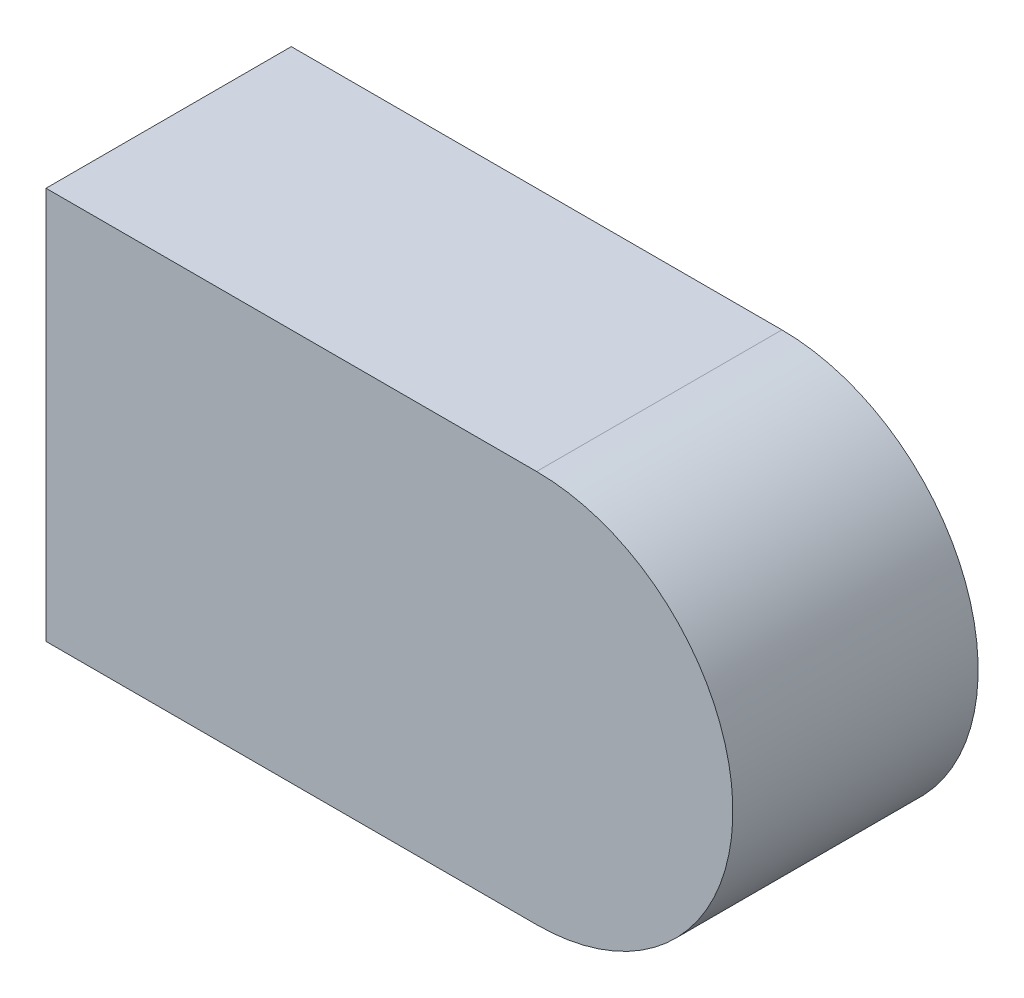
SolidWorks part; units mm, degrees
material "ABS"
ref_plane "Front Plane" through (0, 0, 0) normal (0, 0, 1) x (1, 0, 0)
ref_plane "Top Plane" through (0, 0, 0) normal (0, 1, 0) x (1, 0, 0)
ref_plane "Right Plane" through (0, 0, 0) normal (1, 0, 0) x (0, 0, -1)
sketch "Sketch1" plane through (0, 0, 0) normal (0, 0, 1) x (1, 0, 0)
  line L0 (-250, 192.5) -> (-200, 192.5) construction
  line L1 (-200, 232.5) -> (-250, 232.5) construction
  line L2 (-200, 232.5) -> (-250, 232.5)
  line L3 (-250, 192.5) -> (-200, 192.5)
  line L4 (-250, 232.5) -> (-250, 192.5)
  arc A0 (-200, 192.5) -> (-200, 232.5) centre (-200, 212.5) ccw construction
  arc A2 (-200, 192.5) -> (-200, 232.5) centre (-200, 212.5) ccw
  point P3 (-180, 212.5)
extrude "Boss-Extrude1" add sketch "Sketch1" against normal blind 25
